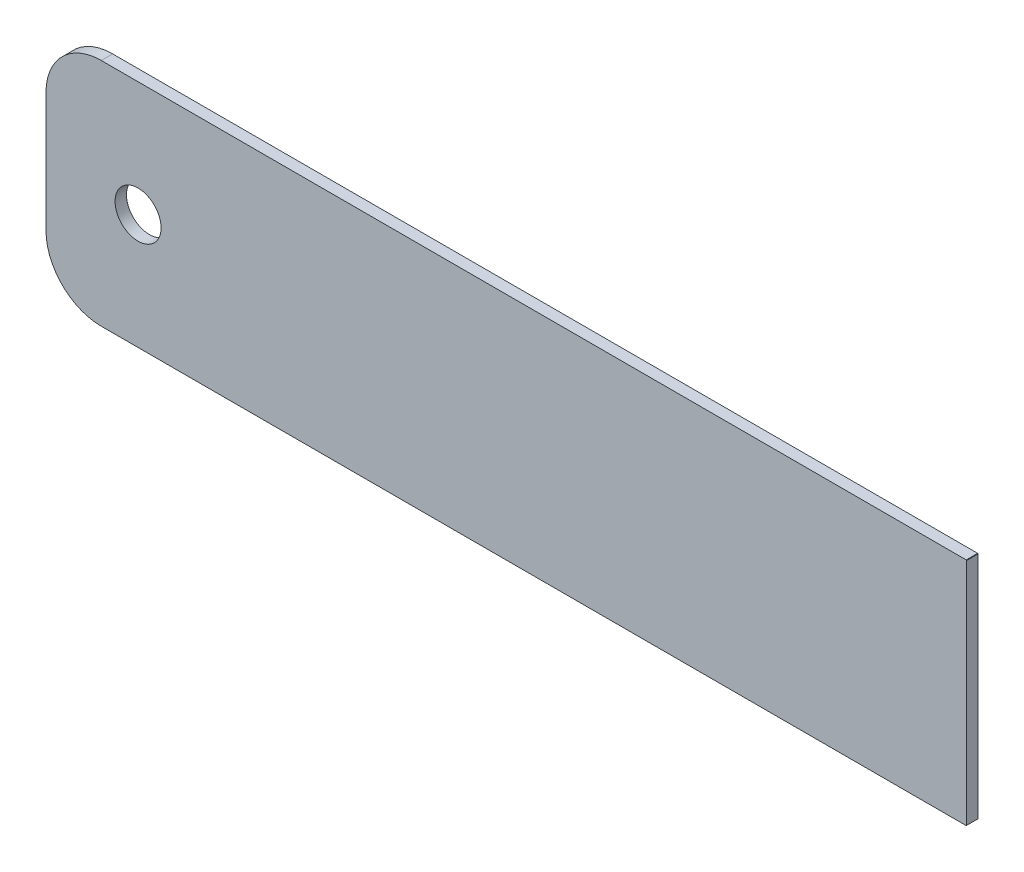
SolidWorks part; units mm, degrees
material "302 SSTL"
ref_plane "Front" through (0, 0, 0) normal (0, 0, 1) x (1, 0, 0)
ref_plane "Top" through (0, 0, 0) normal (0, 1, 0) x (1, 0, 0)
ref_plane "Right" through (0, 0, 0) normal (1, 0, 0) x (0, 0, -1)
sketch "Sketch1" plane through (0, 0, 0) normal (0, 0, 1) x (1, 0, 0)
  line L0 (0, 15.8496) -> (-0.0254, 15.875)
  line L1 (-0.0254, 0) -> (-59.69, 0)
  line L2 (0, 0.0254) -> (0, 15.8496)
  line L3 (-0.0254, 15.875) -> (-59.69, 15.875)
  line L4 (-63.5, 3.81) -> (-63.5, 12.065)
  line L5 (-0.0254, 0) -> (0, 0.0254)
  circle A0 centre (-57.15, 7.9375) radius 1.5875
  arc A1 (-59.69, 15.875) -> (-63.5, 12.065) centre (-59.69, 12.065) ccw
  arc A2 (-59.69, 0) -> (-63.5, 3.81) centre (-59.69, 3.81) cw
  point P9 (-63.5, 15.875)
  point P12 (-63.5, 0)
  point P15 (0, 15.875)
  point P18 (0, 0)
  point P21 (0, 15.875)
  point P24 (0, 0)
  dimension "D3" = 6.35
  dimension "D4" = 3.175
  dimension "D5" = 3.81
  dimension "D1" = 15.875
  dimension "D2" = 63.5
  dimension "D9" = 0.0254
  dimension "D10" = 0.0254
extrude "Extrude1" add sketch "Sketch1" along normal blind 0.7874
